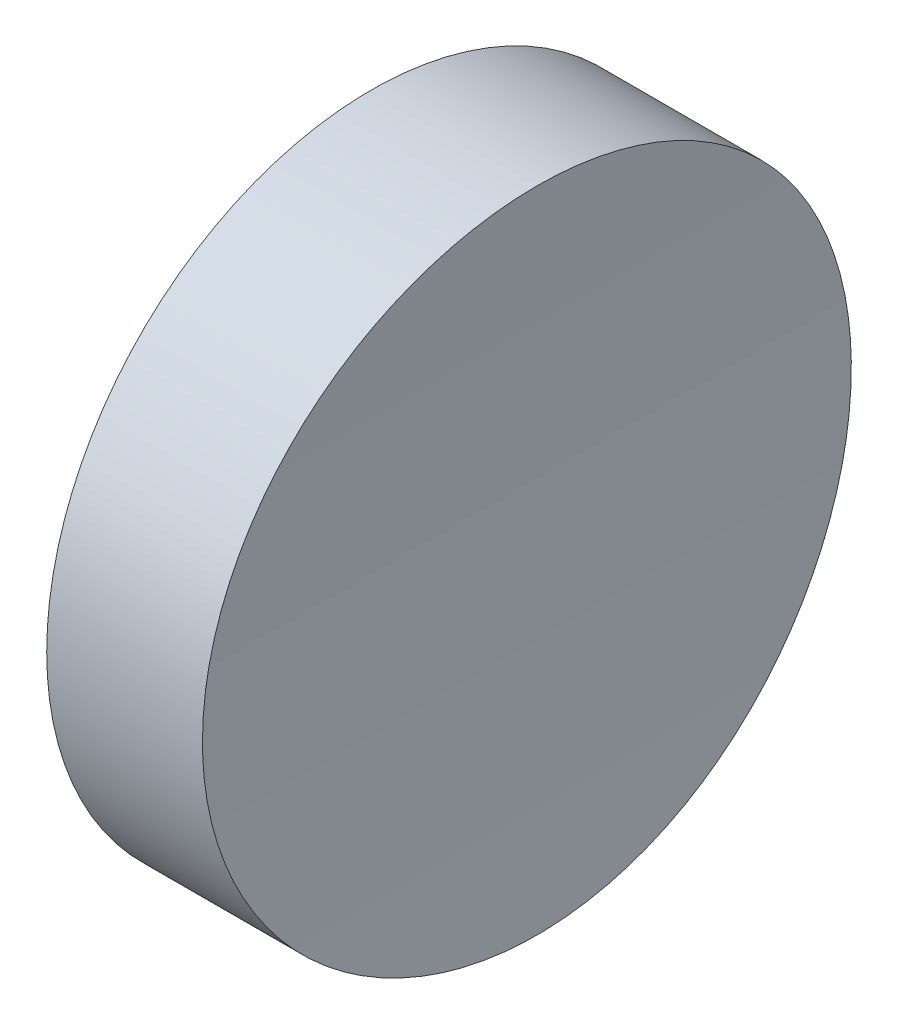
SolidWorks part; units mm, degrees
ref_plane "前视基准面" through (0, 0, 0) normal (0, 0, 1) x (1, 0, 0)
ref_plane "上视基准面" through (0, 0, 0) normal (0, 1, 0) x (1, 0, 0)
ref_plane "右视基准面" through (0, 0, 0) normal (1, 0, 0) x (0, 0, -1)
sketch "草图1" plane through (0, 0, 0) normal (1, 0, 0) x (0, 0, -1)
  circle A0 centre (0, 0) radius 12.5
  dimension "D1" = 25
extrude "凸台-拉伸1" add sketch "草图1" along normal blind 10
sketch "草图2" plane through (0, 0, 0) normal (0, 0, 1) x (1, 0, 0)
  line L0 (0, 0) -> (206, 0) construction
  line L1 (0, 0) -> (6, 0) construction
  circle A0 centre (206, 0) radius 200
  dimension "D1" = 400
  dimension "D2" = 6
extrude "切除-拉伸1" cut sketch "草图2" against normal through all both and the other way through all
